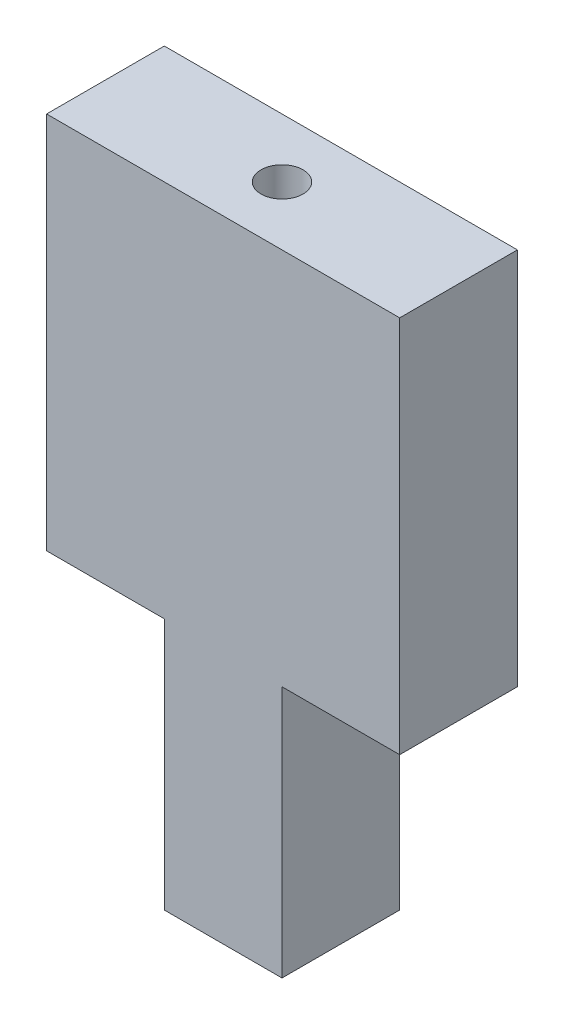
SolidWorks part; units mm, degrees
ref_plane "Front Plane" through (0, 0, 0) normal (0, 0, 1) x (1, 0, 0)
ref_plane "Top Plane" through (0, 0, 0) normal (0, 1, 0) x (1, 0, 0)
ref_plane "Right Plane" through (0, 0, 0) normal (1, 0, 0) x (0, 0, -1)
sketch "Sketch1" plane through (0, 0, 0) normal (0, 1, 0) x (1, 0, 0)
  line L1 (-7, -7) -> (7, -7)
  line L2 (-7, -7) -> (-7, 7)
  line L3 (-7, 7) -> (7, 7)
  line L4 (7, -7) -> (7, 7)
  line L5 (-7, -7) -> (7, 7) construction
  line L6 (-7, 7) -> (7, -7) construction
  point P0 (0, 0)
  dimension "D1" = 14
  dimension "D2" = 14
extrude "Boss-Extrude1" add sketch "Sketch1" along normal blind 75
sketch "Sketch2" plane through (0, 75, 0) normal (0, 1, 0) x (1, 0, 0)
  circle A0 centre (0, 0) radius 2.5
  dimension "D1" = 5
extrude "Cut-Extrude1" cut sketch "Sketch2" against normal blind 30
sketch "Sketch3" plane through (7, 0, 0) normal (1, 0, 0) x (0, 0, -1)
  line L0 (7, 75) -> (7, 0) construction
  line L1 (-7, 75) -> (7, 75)
  line L2 (-7, 75) -> (-7, 30)
  line L3 (-7, 30) -> (7, 30)
  line L4 (7, 75) -> (7, 30)
  dimension "D1" = 45
extrude "Boss-Extrude2" add sketch "Sketch3" along normal blind 14
sketch "Sketch4" plane through (-7, 0, 0) normal (-1, 0, 0) x (0, 0, 1)
  line L5 (7, 75) -> (7, 0) construction
  line L6 (-7, 75) -> (7, 75)
  line L7 (-7, 75) -> (-7, 30)
  line L8 (-7, 30) -> (7, 30)
  line L9 (7, 75) -> (7, 30)
  dimension "D1" = 45
extrude "Boss-Extrude3" add sketch "Sketch4" along normal blind 14
